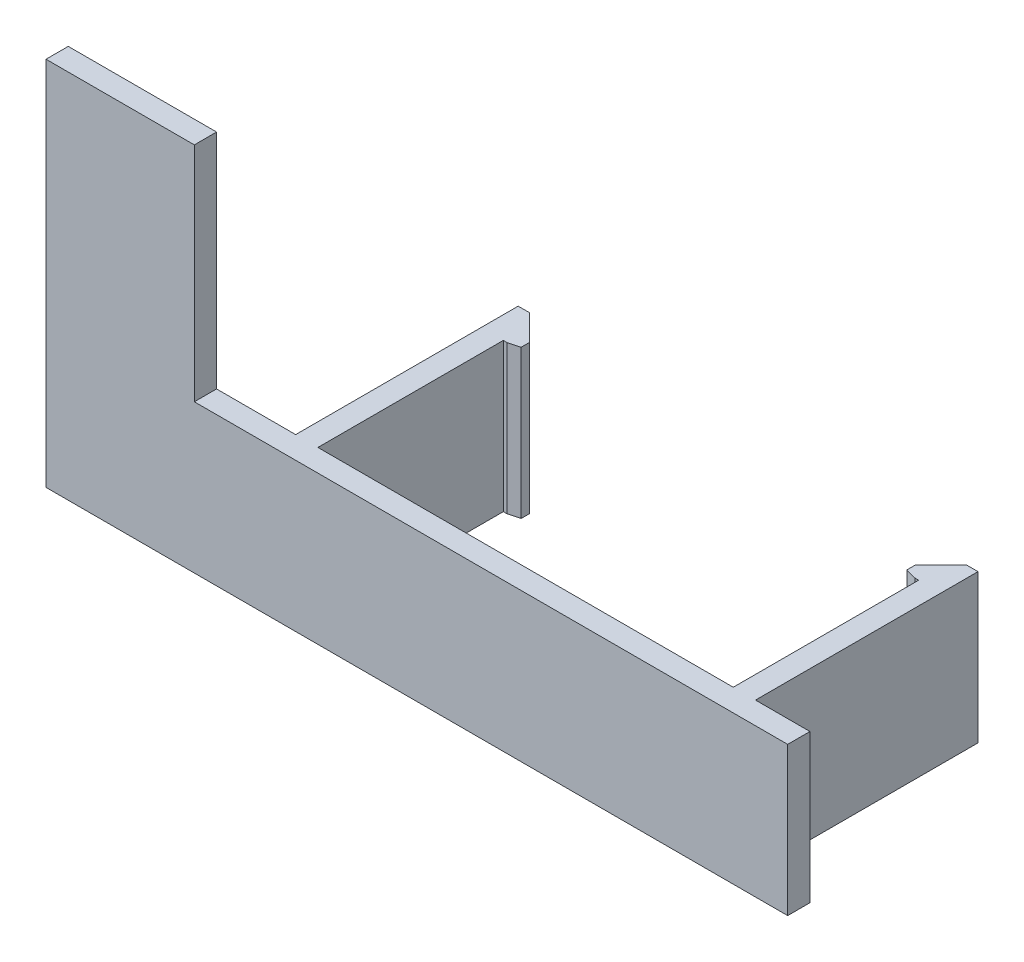
SolidWorks part; units mm, degrees
ref_plane "Plan de face" through (0, 0, 0) normal (0, 0, 1) x (1, 0, 0)
ref_plane "Plan de dessus" through (0, 0, 0) normal (0, 1, 0) x (1, 0, 0)
ref_plane "Plan de droite" through (0, 0, 0) normal (1, 0, 0) x (0, 0, -1)
sketch "Esquisse1" plane through (0, 0, 0) normal (0, 0, 1) x (1, 0, 0)
  line L1 (-50, -50) -> (50, -50)
  line L2 (-50, -50) -> (-50, 50)
  line L3 (-50, 50) -> (50, 50)
  line L4 (50, -50) -> (50, 50)
  line L5 (-50, -50) -> (50, 50) construction
  line L6 (-50, 50) -> (50, -50) construction
  line L7 (130, 130) -> (-30, 130)
  line L8 (130, 130) -> (130, -30)
  line L9 (130, -30) -> (-30, -30)
  line L10 (-30, 130) -> (-30, -30)
  line L11 (130, 130) -> (-30, -30) construction
  line L12 (130, -30) -> (-30, 130) construction
  line L13 (-50, 50) -> (-30, 50)
  line L14 (-50, 50) -> (-50, 0)
  line L15 (-50, 0) -> (-30, 0)
  line L16 (-30, 50) -> (-30, 0)
  point P0 (0, 0)
  dimension "D1" = 100
  dimension "D2" = 100
  dimension "D3" = 160
extrude "Boss.-Extru.1" add sketch "Esquisse1" along normal blind 3 contours L10 L3 L2 L1 L4 L9
sketch "Esquisse2" plane through (0, 0, 0) normal (0, 0, -1) x (-1, 0, 0)
  line L0 (50, -50) -> (-50, -50) construction
  line L1 (-42.6619, -50) -> (-39.6619, -50)
  line L2 (-42.6619, -50) -> (-42.6619, -30)
  line L3 (-42.6619, -30) -> (-39.6619, -30)
  line L4 (-39.6619, -50) -> (-39.6619, -30)
  line L5 (-50, -30) -> (30, -30) construction
  dimension "D1" = 3
extrude "Boss.-Extru.2" add sketch "Esquisse2" along normal blind 30
sketch "Esquisse3" plane through (39.6619, 0, 0) normal (-1, 0, 0) x (0, 0, 1)
  line L0 (-30, -30) -> (0, -30) construction
  line L1 (-30, -50) -> (-25, -50)
  line L2 (-30, -50) -> (-30, -30)
  line L3 (-30, -30) -> (-25, -30)
  line L4 (-25, -50) -> (-25, -30)
  dimension "D1" = 5
extrude "Boss.-Extru.3" add sketch "Esquisse3" along normal blind 2
chamfer "Chanfrein1" distance 3.5 angle 45 1 edges at (37.6619, -40, -30)
chamfer "Chanfrein2" distance 1.5 angle 15 1 edges at (37.6619, -40, -25)
ref_plane "Plan1" through (11.6619, 0, 0) normal (-1, 0, 0) x (0, 0, 1)
mirror "Symétrie1" about plane through (11.6619, 0, 0) normal (-1, 0, 0) of "Chanfrein2", "Chanfrein1", "Boss.-Extru.3", "Boss.-Extru.2"
